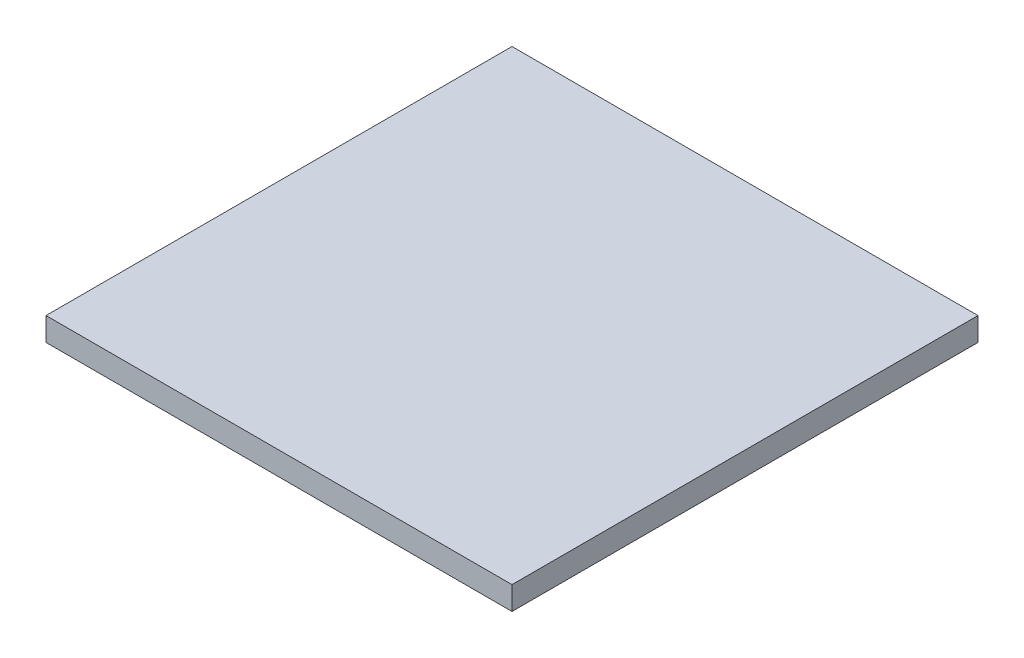
SolidWorks part; units mm, degrees
material "AISI 1020"
ref_plane "Front Plane" through (0, 0, 0) normal (0, 0, 1) x (1, 0, 0)
ref_plane "Top Plane" through (0, 0, 0) normal (0, 1, 0) x (1, 0, 0)
ref_plane "Right Plane" through (0, 0, 0) normal (1, 0, 0) x (0, 0, -1)
sketch "Sketch1" plane through (0, 0, 0) normal (0, 1, 0) x (1, 0, 0)
  line L1 (0, 0) -> (100, 0)
  line L2 (0, 0) -> (0, 100)
  line L3 (0, 100) -> (100, 100)
  line L4 (100, 0) -> (100, 100)
  dimension "D1" = 100
extrude "Boss-Extrude1" add sketch "Sketch1" along normal blind 5
equation "\"lado placa\"=100"
equation "\"D1@Sketch1\"=\"lado placa\""
equation "\"grosor placa\"=5"
equation "\"D1@Boss-Extrude1\"=\"grosor placa\""
